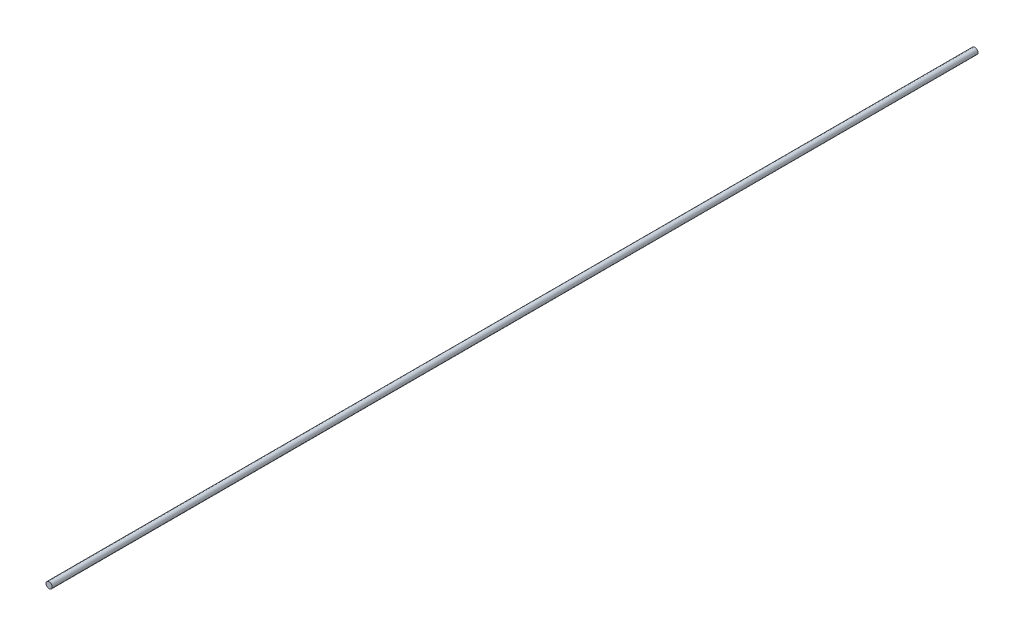
SolidWorks part; units mm, degrees
material "AISI 1020 Steel, Cold Rolled"
ref_plane "Front Plane" through (0, 0, 0) normal (0, 0, 1) x (1, 0, 0)
ref_plane "Top Plane" through (0, 0, 0) normal (0, 1, 0) x (1, 0, 0)
ref_plane "Right Plane" through (0, 0, 0) normal (1, 0, 0) x (0, 0, -1)
sketch "Sketch1" plane through (0, 0, 0) normal (0, 0, 1) x (1, 0, 0)
  circle A0 centre (0, 0) radius 6
  dimension "D1" = 12
extrude "Boss-Extrude1" add sketch "Sketch1" along normal mid plane 1800
cosmetic thread "Cosmetic Thread3" parameters "D2"=6.619
